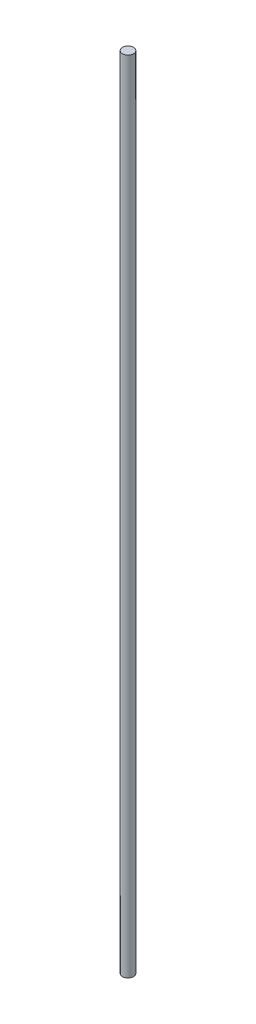
SolidWorks part; units mm, degrees
material "AISI 1020"
ref_plane "Front Plane" through (0, 0, 0) normal (0, 0, 1) x (1, 0, 0)
ref_plane "Top Plane" through (0, 0, 0) normal (0, 1, 0) x (1, 0, 0)
ref_plane "Right Plane" through (0, 0, 0) normal (1, 0, 0) x (0, 0, -1)
sketch "Sketch1" plane through (0, 0, 0) normal (0, 1, 0) x (1, 0, 0)
  circle A0 centre (0, 0) radius 2.5
  dimension "D1" = 5
extrude "Boss-Extrude1" add sketch "Sketch1" along normal blind 360
